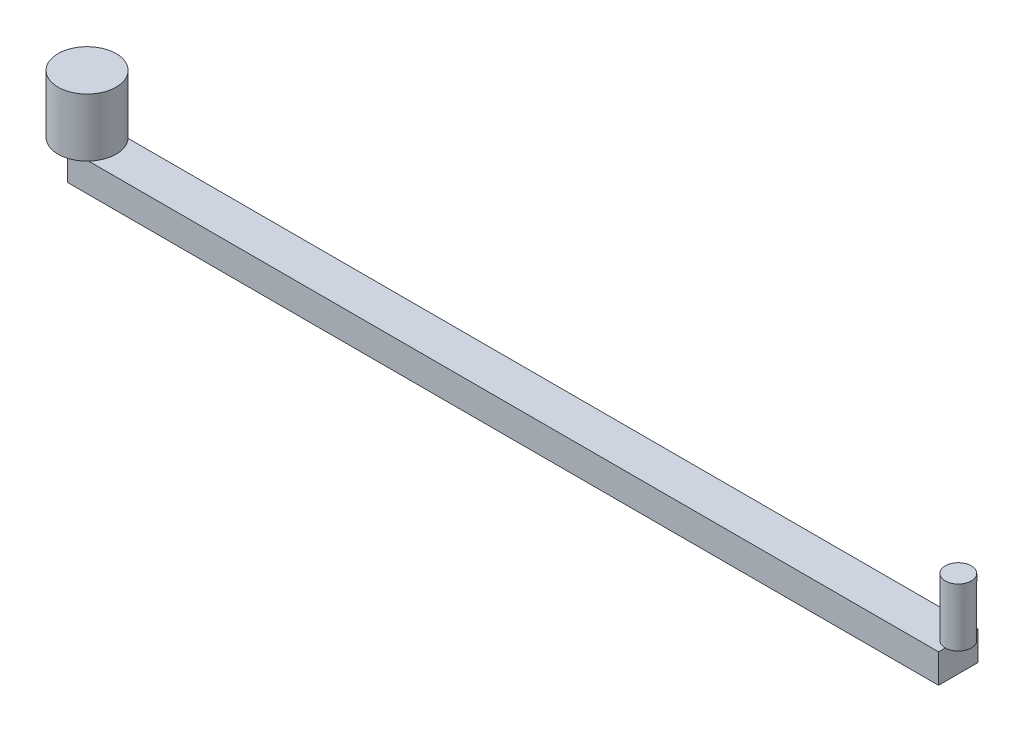
SolidWorks part; units mm, degrees
ref_plane "Front Plane" through (0, 0, 0) normal (0, 0, 1) x (1, 0, 0)
ref_plane "Top Plane" through (0, 0, 0) normal (0, 1, 0) x (1, 0, 0)
ref_plane "Right Plane" through (0, 0, 0) normal (1, 0, 0) x (0, 0, -1)
sketch "Sketch1" plane through (0, 0, 0) normal (0, 1, 0) x (1, 0, 0)
  line L1 (-38.1, -1.7253) -> (38.1, -1.7253)
  line L2 (-38.1, -1.7253) -> (-38.1, 1.7253)
  line L3 (-38.1, 1.7253) -> (38.1, 1.7253)
  line L4 (38.1, -1.7253) -> (38.1, 1.7253)
  line L5 (-38.1, -1.7253) -> (38.1, 1.7253) construction
  line L6 (-38.1, 1.7253) -> (38.1, -1.7253) construction
  point P0 (0, 0)
  dimension "3" = 76.2
extrude "Boss-Extrude1" add sketch "Sketch1" along normal blind 2.54
sketch "Sketch2" plane through (0, 2.54, 0) normal (0, 1, 0) x (1, 0, 0)
  line L0 (-38.1, 1.7253) -> (-38.1, -1.7253) construction
  circle A0 centre (-38.1, 0) radius 2.54
  dimension "D1" = 5.08
extrude "Boss-Extrude2" add sketch "Sketch2" along normal blind 5.08
sketch "Sketch3" plane through (0, 2.54, 0) normal (0, 1, 0) x (1, 0, 0)
  line L0 (38.1, -1.7253) -> (38.1, 1.7253) construction
  circle A0 centre (38.1, 0) radius 1.143
  dimension "D1" = 2.286
extrude "Boss-Extrude3" add sketch "Sketch3" along normal blind 5.08
